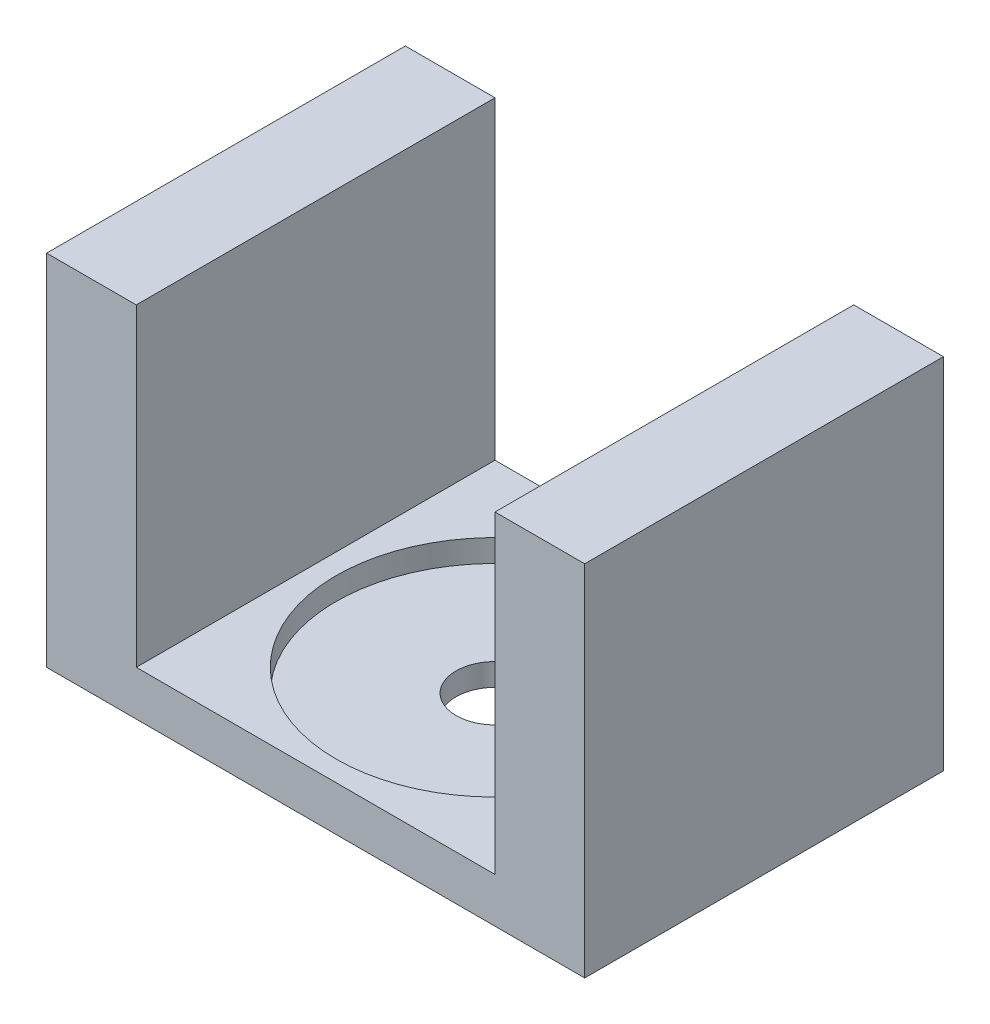
SolidWorks part; units mm, degrees
material "6063-O"
ref_plane "Front" through (0, 0, 0) normal (0, 0, 1) x (1, 0, 0)
ref_plane "Top" through (0, 0, 0) normal (0, 1, 0) x (1, 0, 0)
ref_plane "Right" through (0, 0, 0) normal (1, 0, 0) x (0, 0, -1)
sketch "Sketch1" plane through (0, 0, 0) normal (0, 0, 1) x (1, 0, 0)
  line L0 (0, -703.9235) -> (0, 0) construction
  line L13 (0, 6.35) -> (0, 34852.6286) construction
  line L14 (38.1, 0) -> (-38.1, 0)
  line L16 (25.4, 6.35) -> (-25.4, 6.35)
  line L19 (-25.4, 6.35) -> (-25.4, 50.8)
  line L20 (-25.4, 50.8) -> (-38.1, 50.8)
  line L21 (-38.1, 0) -> (-38.1, 50.8)
  line L22 (38.1, 0) -> (38.1, 50.8)
  line L23 (25.4, 50.8) -> (38.1, 50.8)
  line L24 (25.4, 6.35) -> (25.4, 50.8)
  dimension "D1" = 38.1
  dimension "D2" = 50.8
  dimension "D3" = 12.7
  dimension "D4" = 44.45
  dimension "D5" = 6.35
extrude "Boss-Extrude1" add sketch "Sketch1" along normal blind 50.8
sketch "Sketch2" plane through (0, 6.35, 0) normal (0, 1, 0) x (1, 0, 0)
  line L0 (0, 0) -> (0, -50.8) construction
  line L1 (25.4, -50.8) -> (-25.4, -50.8) construction
  circle A0 centre (0, -25.4) radius 22.5044
  dimension "D1" = 45.0088
extrude "Cut-Extrude1" cut sketch "Sketch2" against normal blind 3.175
sketch "Sketch3" plane through (0, 3.175, 0) normal (0, 1, 0) x (1, 0, 0)
  line L0 (0, 0) -> (0, -50.8) construction
  line L1 (25.4, -50.8) -> (-25.4, -50.8) construction
  circle A0 centre (0, -25.4) radius 5.5
  dimension "D1" = 11
extrude "Cut-Extrude2" cut sketch "Sketch3" against normal through all
